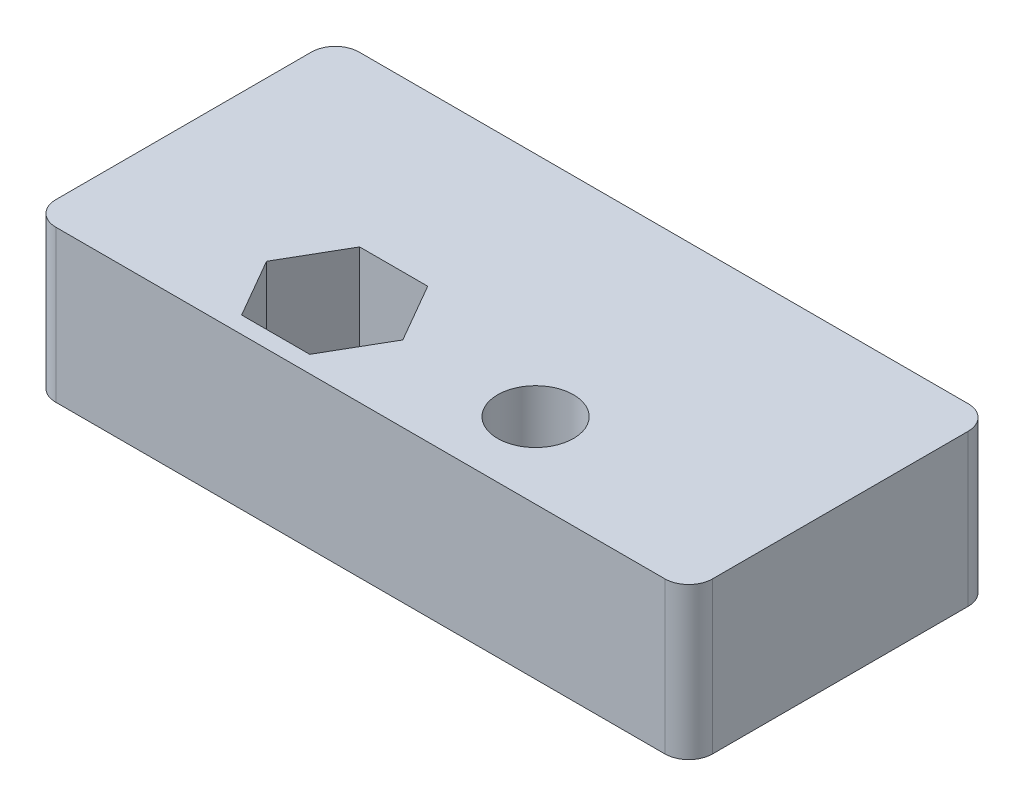
SolidWorks part; units mm, degrees
material "Balsa"
ref_plane "Front Plane" through (0, 0, 0) normal (0, 0, 1) x (1, 0, 0)
ref_plane "Top Plane" through (0, 0, 0) normal (0, 1, 0) x (1, 0, 0)
ref_plane "Right Plane" through (0, 0, 0) normal (1, 0, 0) x (0, 0, -1)
sketch "Sketch1" plane through (0, 0, 0) normal (0, 1, 0) x (1, 0, 0)
  line L1 (0, 0) -> (27.5, 0)
  line L2 (0, 0) -> (0, 12.7)
  line L3 (0, 12.7) -> (27.5, 12.7)
  line L4 (27.5, 0) -> (27.5, 12.7)
  line L5 (12.3523, 3.175) -> (10.9261, 5.6452)
  line L6 (10.9261, 5.6452) -> (8.0739, 5.6452)
  line L7 (8.0739, 5.6452) -> (6.6477, 3.175)
  line L8 (6.6477, 3.175) -> (8.0739, 0.7049)
  line L9 (8.0739, 0.7049) -> (10.9261, 0.7049)
  line L10 (10.9261, 0.7049) -> (12.3523, 3.175)
  circle A0 centre (9.5, 3.175) radius 1.75 construction
  circle A1 centre (17.9125, 3.175) radius 1.5875
  circle A2 centre (9.5, 3.175) radius 2.4701 construction
  dimension "D3" = 3.175
  dimension "D4" = 3.5
  dimension "D1" = 27.5
  dimension "D2" = 12.7
  dimension "D5" = 9.5
  dimension "D6" = 3.175
  dimension "D7" = 3.175
  dimension "D8" = 8.4125
  dimension "D9" = 4.9403
extrude "Boss-Extrude1" add sketch "Sketch1" along normal blind 6.35
fillet "Fillet1" radius 1 4 edges at (0, 3.175, 0) (0, 3.175, -12.7) (27.5, 3.175, -12.7) (27.5, 3.175, 0)
other "Move Face1" [suppressed] parameters "D1"=0.08
